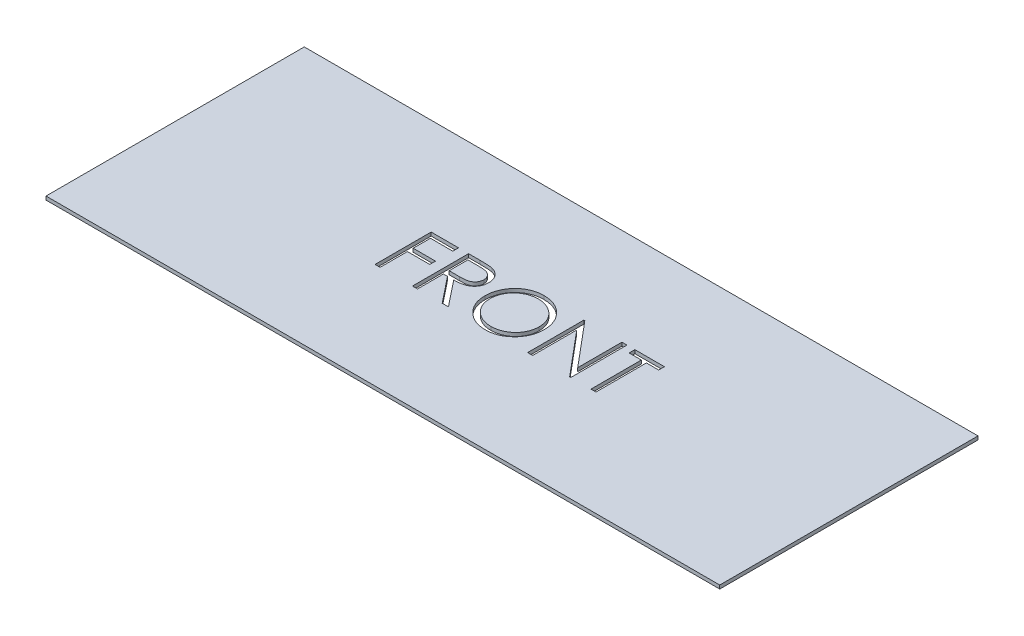
SolidWorks part; units mm, degrees
material "ABS"
ref_plane "Front Plane" through (0, 0, 0) normal (0, 0, 1) x (1, 0, 0)
ref_plane "Top Plane" through (0, 0, 0) normal (0, 1, 0) x (1, 0, 0)
ref_plane "Right Plane" through (0, 0, 0) normal (1, 0, 0) x (0, 0, -1)
sketch "Sketch1" plane through (0, 0, 0) normal (0, 1, 0) x (1, 0, 0)
  line L1 (-19.05, -7.3025) -> (19.05, -7.3025)
  line L2 (-19.05, -7.3025) -> (-19.05, 7.3025)
  line L3 (-19.05, 7.3025) -> (19.05, 7.3025)
  line L4 (19.05, -7.3025) -> (19.05, 7.3025)
  line L5 (-19.05, -7.3025) -> (19.05, 7.3025) construction
  line L6 (-19.05, 7.3025) -> (19.05, -7.3025) construction
  point P0 (0, 0)
  dimension "D1" = 14.605
  dimension "D2" = 38.1
extrude "Boss-Extrude1" add sketch "Sketch1" along normal blind 0.2
sketch "Sketch2" plane through (0, 0.2, 0) normal (0, 1, 0) x (1, 0, 0)
  text T0 "FRONT"
extrude "Cut-Extrude1" cut sketch "Sketch2" against normal blind 0.2
